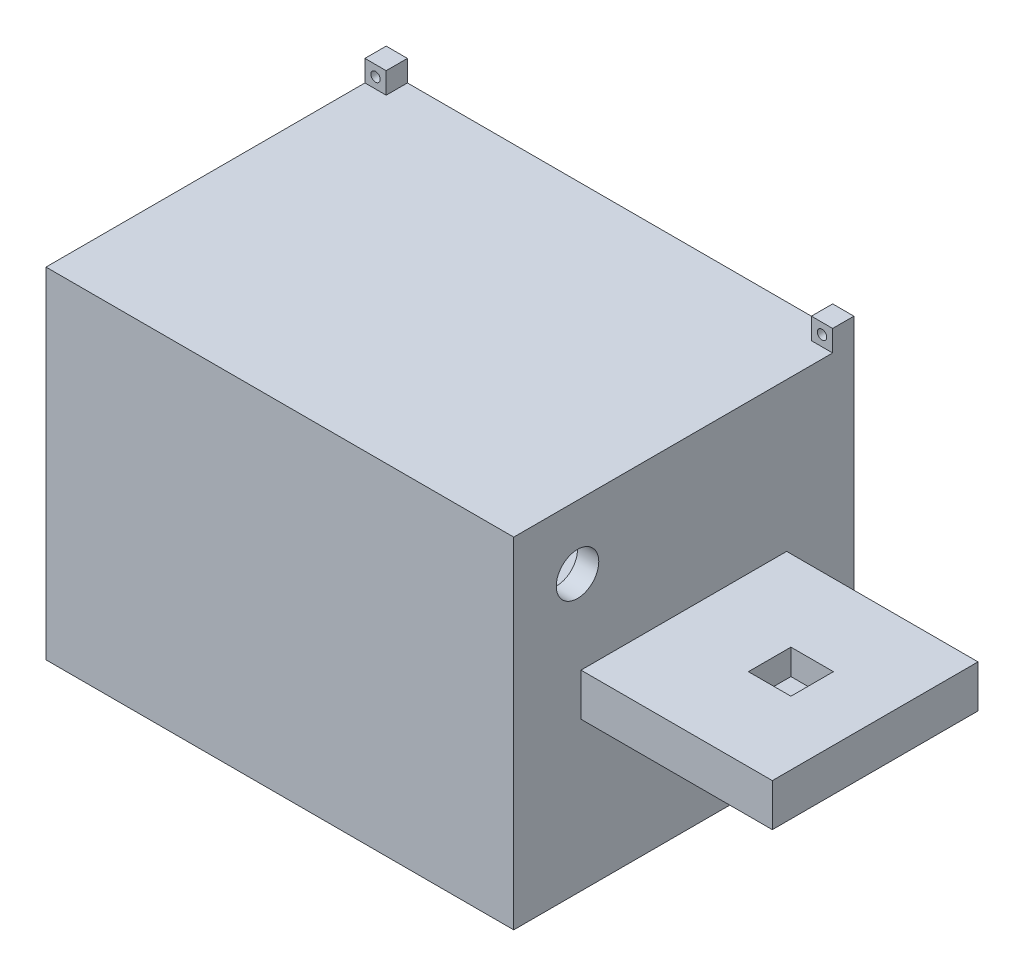
SolidWorks part; units mm, degrees
ref_plane "前基準面" through (0, 0, 0) normal (0, 0, 1) x (1, 0, 0)
ref_plane "上基準面" through (0, 0, 0) normal (0, 1, 0) x (1, 0, 0)
ref_plane "右基準面" through (0, 0, 0) normal (1, 0, 0) x (0, 0, -1)
sketch "草圖1" plane through (0, 0, 0) normal (0, 0, 1) x (1, 0, 0)
  line L0 (-75.5089, 45.5899) -> (79.4911, 45.5899)
  line L4 (-75.5089, 5.5899) -> (79.4911, 5.5899) construction
  line L5 (-75.5089, 45.5899) -> (-75.5089, -34.4101)
  line L6 (79.4911, 45.5899) -> (79.4911, -34.4101)
  line L7 (-75.5089, -34.4101) -> (79.4911, -34.4101)
  dimension "D1" = 155
  dimension "D2" = 80
extrude "填料-伸長1" add sketch "草圖1" along normal blind 80
sketch "草圖5" plane through (0, -34.4101, 0) normal (0, -1, 0) x (1, 0, 0)
  line L0 (34.4911, 80) -> (34.4911, 0)
  line L1 (-75.5089, 80) -> (79.4911, 80) construction
  line L2 (-75.5089, 0) -> (79.4911, 0) construction
  line L3 (34.4911, 0) -> (79.4911, 0)
  line L4 (79.4911, 0) -> (79.4911, 80)
  line L5 (79.4911, 80) -> (34.4911, 80)
  dimension "D1" = 45
sketch "草圖6" plane through (0, 45.5899, 0) normal (0, 1, 0) x (1, 0, 0)
  line L0 (34.4911, 0) -> (34.4911, -80)
  line L1 (34.4911, -80) -> (79.4911, -80)
  line L2 (79.4911, -80) -> (79.4911, 0)
  line L3 (79.4911, 0) -> (34.4911, 0)
extrude "除料-伸長1" cut sketch "草圖6" against normal blind 35
extrude "除料-伸長2" cut sketch "草圖5" against normal blind 35
sketch "草圖7" plane through (0, 0, 0) normal (0, 0, 1) x (1, 0, 0)
  line L0 (-75.5089, 5.5899) -> (79.4911, 5.5899) construction
  line L1 (-75.5089, 45.5899) -> (-75.5089, -34.4101) construction
  line L2 (79.4911, 0.5899) -> (79.4911, 10.5899) construction
  line L3 (-70.5089, -29.4101) -> (-70.5089, 40.5899)
  line L4 (-70.5089, 40.5899) -> (29.4911, 40.5899)
  line L5 (29.4911, 40.5899) -> (29.4911, -29.4101)
  line L6 (-70.5089, -29.4101) -> (29.4911, -29.4101)
  line L7 (34.4911, 45.5899) -> (-75.5089, 45.5899) construction
  line L8 (34.4911, 0.5899) -> (34.4911, -34.4101) construction
  point P11 (29.4911, 5.5899)
  point P12 (-70.5089, 5.5899)
  dimension "D1" = 5
  dimension "D2" = 5
  dimension "D3" = 5
extrude "除料-伸長3" cut sketch "草圖7" along normal blind 75
sketch "草圖8" plane through (0, 0, 0) normal (0, 0, -1) x (-1, 0, 0)
  line L0 (-79.4911, 5.5899) -> (75.5089, 5.5899) construction
  line L1 (-79.4911, 0.5899) -> (-79.4911, 10.5899) construction
  line L2 (75.5089, 45.5899) -> (75.5089, -34.4101) construction
  line L3 (-33.3911, 44.4899) -> (-33.3911, -33.3101)
  line L4 (-33.3911, 44.4899) -> (74.4089, 44.4899)
  line L5 (74.4089, 44.4899) -> (74.4089, -33.3101)
  line L7 (71.6089, -30.5101) -> (71.6089, 41.6899)
  line L8 (71.6089, 41.6899) -> (-30.5911, 41.6899)
  line L9 (-30.5911, 41.6899) -> (-30.5911, -30.5101)
  line L11 (-34.4911, 45.5899) -> (75.5089, 45.5899) construction
  line L12 (-34.4911, 10.5899) -> (-34.4911, 45.5899) construction
  line L13 (71.6089, -30.5101) -> (-30.5911, -30.5101)
  line L14 (-33.3911, -33.3101) -> (74.4089, -33.3101)
  dimension "D2" = 2.8
  dimension "D3" = 2.8
  dimension "D4" = 1.1
  dimension "D5" = 1.1
  dimension "D6" = 1.1
extrude "除料-伸長4" cut sketch "草圖8" against normal blind 10
ref_plane "平面1" through (34.4911, 0, 0) normal (1, 0, 0) x (0, 0, -1)
sketch "草圖9" plane through (34.4911, 0, 0) normal (1, 0, 0) x (0, 0, -1)
  line L0 (-80, 5.5899) -> (0, 5.5899) construction
  line L1 (-80, 0.5899) -> (-80, 10.5899) construction
  line L2 (0, 0.5899) -> (0, 10.5899) construction
  line L3 (0, 41.6899) -> (0, -30.5101) construction
  line L4 (-80, 10.5899) -> (-80, 45.5899) construction
  line L5 (0, 10.5899) -> (-80, 10.5899) construction
  line L6 (0, 0.5899) -> (-80, 0.5899) construction
  circle A2 centre (-65, 30.5899) radius 5
  circle A3 centre (-20, -19.4101) radius 5
  dimension "D1" = 10
  dimension "D2" = 10
  dimension "D3" = 20
  dimension "D4" = 15
  dimension "D5" = 20
  dimension "D6" = 20
extrude "除料-伸長5" cut sketch "草圖9" against normal blind 10
ref_plane "平面2" through (0, -34.4101, 0) normal (0, -1, 0) x (-1, 0, 0)
sketch "草圖10" plane through (0, -34.4101, 0) normal (0, -1, 0) x (-1, 0, 0)
  line L0 (75.5089, 0) -> (-34.4911, 0) construction
  line L1 (14.0089, -15) -> (35.5089, -15)
  line L2 (14.0089, -15) -> (14.0089, -30)
  line L3 (14.0089, -30) -> (35.5089, -30)
  line L4 (35.5089, -15) -> (35.5089, -30)
  line L5 (75.5089, -80) -> (75.5089, 0) construction
  point P6 (24.7589, -15)
  dimension "D1" = 21.5
  dimension "D2" = 15
  dimension "D3" = 15
  dimension "D4" = 40
extrude "除料-伸長6" cut sketch "草圖10" against normal blind 10
sketch "草圖12" plane through (34.4911, 0, 0) normal (1, 0, 0) x (0, 0, -1)
  line L0 (-40, 45.5899) -> (-40, -34.4101) construction
  line L1 (0, 45.5899) -> (-80, 45.5899) construction
  line L2 (-80, -34.4101) -> (0, -34.4101) construction
  line L3 (-80, 10.5899) -> (-80, 0.5899)
  line L4 (-80, 0.5899) -> (-64.1831, 0.5899)
  line L5 (0, 0.5899) -> (-80, 0.5899) construction
  line L6 (-64.1831, 0.5899) -> (-64.1831, 10.5899)
  line L7 (0, 10.5899) -> (-80, 10.5899) construction
  line L8 (-64.1831, 10.5899) -> (-80, 10.5899)
  line L9 (-15.8169, 10.5899) -> (0, 10.5899)
  line L10 (0, 10.5899) -> (0, 0.5899)
  line L11 (0, 0.5899) -> (-15.8169, 0.5899)
  line L12 (-15.8169, 0.5899) -> (-15.8169, 10.5899)
extrude "除料-伸長7" cut sketch "草圖12" along normal blind 45
ref_plane "平面3" through (0, 0.5899, 0) normal (0, -1, 0) x (-1, 0, 0)
sketch "草圖14" plane through (0, 0.5899, 0) normal (0, -1, 0) x (-1, 0, 0)
  line L4 (-79.4911, -40) -> (-70.9929, -40) construction
  line L5 (-79.4911, -15.8169) -> (-79.4911, -64.1831) construction
  line L6 (-58.1372, -35.1028) -> (-41.646, -38.5)
  line L7 (-58.1372, -44.8972) -> (-41.646, -41.5)
  line L8 (-59.146, -45) -> (-59.146, -45.1799) construction
  line L9 (-60.1548, -44.8972) -> (-76.646, -41.5)
  line L10 (-60.1548, -35.1028) -> (-76.646, -38.5)
  line L11 (-49.9929, -40) -> (-38.9929, -40) construction
  line L12 (-40.146, -40) -> (-28.4331, -40) construction
  arc A2 (-60.1548, -44.8972) -> (-58.1372, -44.8972) centre (-59.146, -40) ccw
  arc A3 (-41.646, -41.5) -> (-41.646, -38.5) centre (-41.646, -40) ccw
  arc A5 (-76.646, -41.5) -> (-76.646, -38.5) centre (-76.646, -40) cw
  arc A6 (-58.1372, -35.1028) -> (-60.1548, -35.1028) centre (-59.146, -40) ccw
  dimension "D1" = 10
  dimension "D2" = 3
extrude "除料-伸長8" cut sketch "草圖14" against normal blind 3
ref_plane "平面4" through (0, 10.5899, 0) normal (0, 1, 0) x (1, 0, 0)
sketch "草圖15" plane through (0, 10.5899, 0) normal (0, 1, 0) x (1, 0, 0)
  line L0 (34.4911, -15.8169) -> (34.4911, -64.1831) construction
  line L1 (54.4911, -34.8169) -> (64.4911, -34.8169)
  line L2 (54.4911, -34.8169) -> (54.4911, -44.8169)
  line L3 (54.4911, -44.8169) -> (64.4911, -44.8169)
  line L4 (64.4911, -34.8169) -> (64.4911, -44.8169)
  line L5 (79.4911, -15.8169) -> (34.4911, -15.8169) construction
  dimension "D1" = 10
  dimension "D2" = 10
  dimension "D3" = 20
  dimension "D4" = 19
extrude "除料-伸長9" cut sketch "草圖15" against normal blind 6
sketch "草圖17" plane through (0, 0.5899, 0) normal (0, -1, 0) x (-1, 0, 0)
  line L0 (-78.146, -40) -> (-40.146, -40) construction
  line L1 (-59.146, -45) -> (-59.146, -35) construction
  arc A0 (-76.646, -38.5) -> (-76.646, -41.5) centre (-76.646, -40) ccw construction
  arc A1 (-41.646, -41.5) -> (-41.646, -38.5) centre (-41.646, -40) ccw construction
  arc A2 (-60.1548, -44.8972) -> (-58.1372, -44.8972) centre (-59.146, -40) ccw construction
  arc A3 (-58.1372, -35.1028) -> (-60.1548, -35.1028) centre (-59.146, -40) ccw construction
  circle A4 centre (-59.146, -40) radius 1.0953
extrude "除料-伸長11" cut sketch "草圖17" against normal blind 7
sketch "草圖18" plane through (0, 0, 0) normal (0, 0, 1) x (1, 0, 0)
  line L0 (79.4911, 5.5899) -> (-75.5089, 5.5899) construction
  line L1 (79.4911, 10.5899) -> (79.4911, 0.5899) construction
  line L2 (-75.5089, 45.5899) -> (-75.5089, -34.4101) construction
  line L3 (34.4911, 45.5899) -> (-75.5089, 45.5899) construction
  line L4 (-20.5089, 45.5899) -> (-20.5089, -34.4101) construction
  line L5 (-44, -34.4101) -> (44, -34.4101) construction
  line L6 (34.4911, -43.147) -> (34.4911, 43.147) construction
  line L7 (34.4911, 45.5899) -> (29.4911, 45.5899)
  line L8 (34.4911, 45.5899) -> (34.4911, 50.5899)
  line L9 (34.4911, 50.5899) -> (29.4911, 50.5899)
  line L10 (29.4911, 45.5899) -> (29.4911, 50.5899)
  line L11 (34.4911, 48.0899) -> (29.4911, 48.0899) construction
  line L12 (31.9911, 50.5899) -> (31.9911, 45.5899) construction
  line L13 (-75.5089, 50.5899) -> (-70.5089, 50.5899)
  line L14 (-70.5089, 45.5899) -> (-70.5089, 50.5899)
  line L15 (-75.5089, 45.5899) -> (-70.5089, 45.5899)
  line L16 (-75.5089, 45.5899) -> (-75.5089, 50.5899)
  line L17 (-75.5089, -34.4101) -> (-70.5089, -34.4101)
  line L18 (-75.5089, -34.4101) -> (-75.5089, -39.4101)
  line L19 (-75.5089, -39.4101) -> (-70.5089, -39.4101)
  line L20 (-70.5089, -34.4101) -> (-70.5089, -39.4101)
  line L21 (34.4911, -34.4101) -> (29.4911, -34.4101)
  line L22 (29.4911, -34.4101) -> (29.4911, -39.4101)
  line L23 (34.4911, -39.4101) -> (29.4911, -39.4101)
  line L24 (34.4911, -34.4101) -> (34.4911, -39.4101)
  circle A0 centre (31.9911, 48.0899) radius 1.1
  circle A1 centre (-73.0089, 48.0899) radius 1.1
  circle A2 centre (-73.0089, -36.9101) radius 1.1
  circle A3 centre (31.9911, -36.9101) radius 1.1
  dimension "D3" = 2.2
  dimension "D1" = 5
  dimension "D2" = 5
extrude "填料-伸長2" add sketch "草圖18" along normal blind 5
